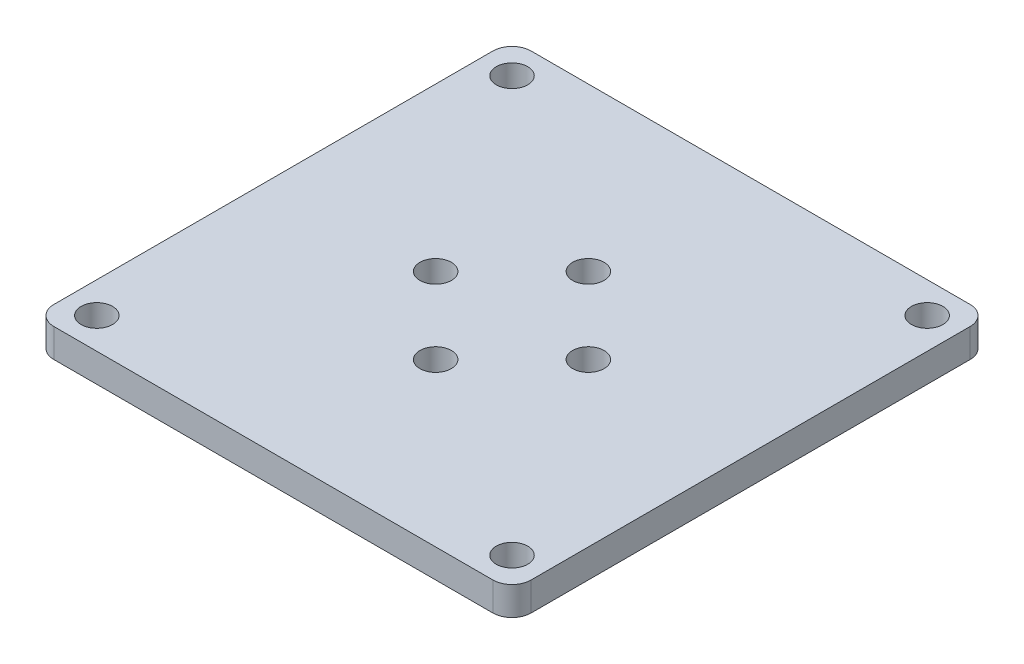
SolidWorks part; units mm, degrees
ref_plane "前视基准面" through (0, 0, 0) normal (0, 0, 1) x (1, 0, 0)
ref_plane "上视基准面" through (0, 0, 0) normal (0, 1, 0) x (1, 0, 0)
ref_plane "右视基准面" through (0, 0, 0) normal (1, 0, 0) x (0, 0, -1)
other "Configuration Table"
sketch "草图1" plane through (0, 0, 0) normal (0, 1, 0) x (1, 0, 0)
  line L1 (-25, -25) -> (25, -25)
  line L2 (-25, -25) -> (-25, 25)
  line L3 (-25, 25) -> (25, 25)
  line L4 (25, -25) -> (25, 25)
  line L5 (-25, -25) -> (25, 25) construction
  line L6 (-25, 25) -> (25, -25) construction
  circle A0 centre (21.75, 21.75) radius 1.65
  circle A1 centre (-21.75, 21.75) radius 1.65
  circle A2 centre (21.75, -21.75) radius 1.65
  circle A3 centre (-21.75, -21.75) radius 1.65
  circle A5 centre (8, 0) radius 1.65
  circle A6 centre (0, 8) radius 1.65
  circle A7 centre (-8, 0) radius 1.65
  circle A8 centre (0, -8) radius 1.65
  point P0 (0, 0)
  dimension "D3" = 3.3
  dimension "D4" = 3.3
  dimension "D7" = 3.3
  dimension "D8" = 3.3
  dimension "D13" = 3.3
  dimension "D14" = 3.3
  dimension "D15" = 3.3
  dimension "D16" = 3.3
  dimension "D1" = 50
  dimension "D2" = 50
  dimension "D5" = 43.5
  dimension "D6" = 3.25
  dimension "D9" = 43.5
  dimension "D10" = 43.5
  dimension "D11" = 43.5
  dimension "D12" = 3.25
  dimension "D17" = 16
  dimension "D18" = 16
  dimension "D19" = 25
  dimension "D20" = 25
  dimension "D21" = 17
  dimension "D22" = 17
  dimension "D23" = 25
  dimension "D24" = 25
extrude "凸台-拉伸2" add sketch "草图1" along normal blind 3
fillet "圆角1" radius 2 1 edges at (25, 1.5, 25)
fillet "圆角2" radius 2 1 edges at (25, 1.5, -25)
fillet "圆角3" radius 2 1 edges at (-25, 1.5, -25)
fillet "圆角4" radius 2 1 edges at (-25, 1.5, 25)
